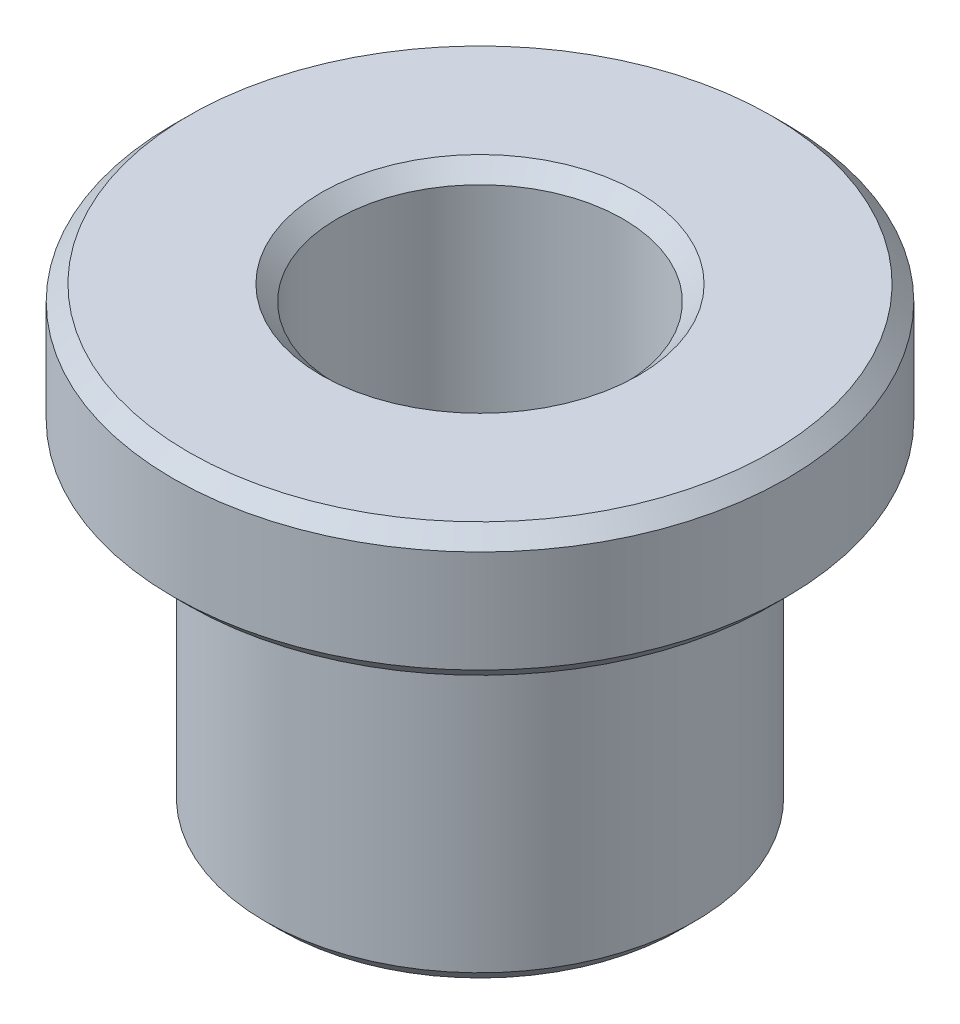
SolidWorks part; units mm, degrees
material "铝青铜"
ref_plane "前视基准面" through (0, 0, 0) normal (0, 0, 1) x (1, 0, 0)
ref_plane "上视基准面" through (0, 0, 0) normal (0, 1, 0) x (1, 0, 0)
ref_plane "右视基准面" through (0, 0, 0) normal (1, 0, 0) x (0, 0, -1)
other "Configuration Table"
sketch "草图1" plane through (0, 0, 0) normal (0, 1, 0) x (1, 0, 0)
  circle A0 centre (0, 0) radius 21
  dimension "D1" = 42
extrude "凸台-拉伸1" add sketch "草图1" along normal blind 32
sketch "草图2" plane through (0, 32, 0) normal (0, 1, 0) x (1, 0, 0)
  circle A0 centre (0, 0) radius 30
  dimension "D1" = 60
extrude "凸台-拉伸2" add sketch "草图2" along normal blind 13
sketch "草图3" plane through (0, 45, 0) normal (0, 1, 0) x (1, 0, 0)
  circle A0 centre (0, 0) radius 14
  dimension "D1" = 28
extrude "切除-拉伸1" cut sketch "草图3" against normal through all
chamfer "倒角1" distance 1.5 angle 45 5 edges at (0, 0, 14) (0, 0, 21) (0, 32, 30) (0, 45, 30) (0, 45, 14)
